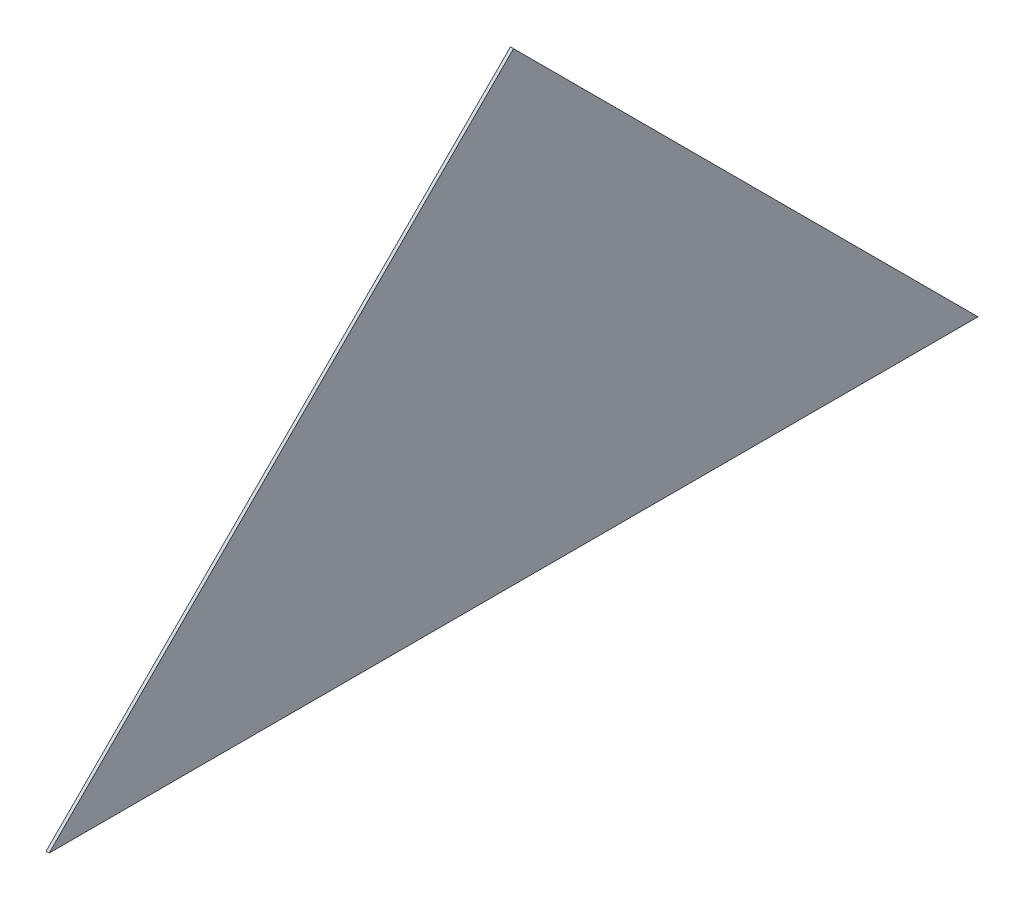
SolidWorks part; units mm, degrees
ref_plane "前视基准面" through (0, 0, 0) normal (0, 0, 1) x (1, 0, 0)
ref_plane "上视基准面" through (0, 0, 0) normal (0, 1, 0) x (1, 0, 0)
ref_plane "右视基准面" through (0, 0, 0) normal (1, 0, 0) x (0, 0, -1)
sketch "草图1" plane through (0, 0, 0) normal (1, 0, 0) x (0, 0, -1)
  line L0 (0, 0) -> (3000, 0)
  line L5 (1500, 1500) -> (0, 0)
  line L6 (1500, 1500) -> (3000, 0)
  point P3 (1500, 1500)
  point P4 (1500, -22.0588)
  point P8 (1519.369, 172.6839)
  point P9 (1503.9643, 1379.3893)
  dimension "D1" = 3000
  dimension "D2" = 2121.3204
extrude "凸台-拉伸1" add sketch "草图1" along normal blind 10
